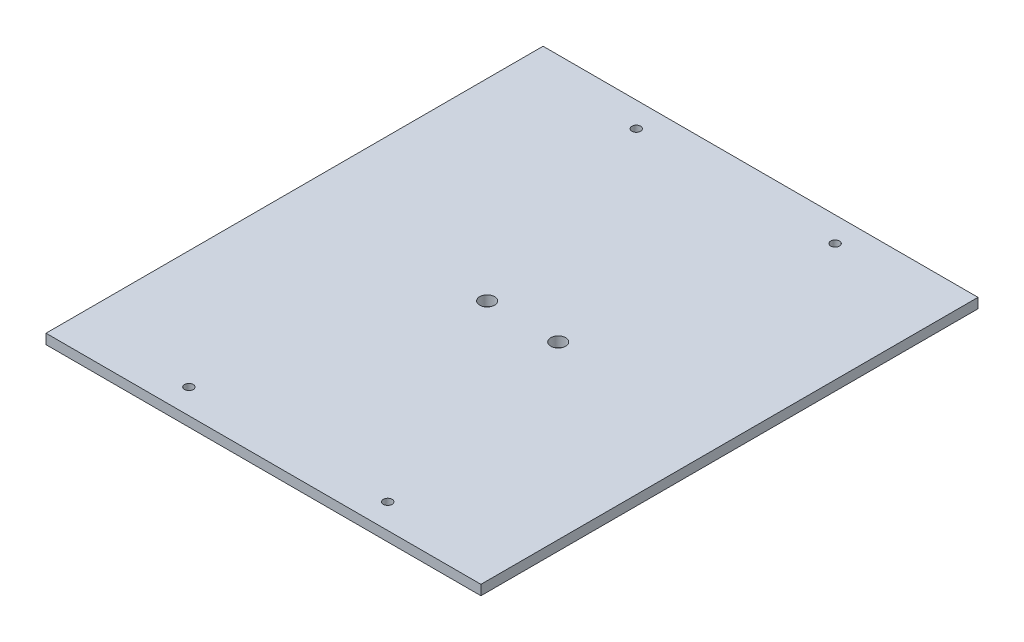
SolidWorks part; units mm, degrees
ref_plane "Front Plane" through (0, 0, 0) normal (0, 0, 1) x (1, 0, 0)
ref_plane "Top Plane" through (0, 0, 0) normal (0, 1, 0) x (1, 0, 0)
ref_plane "Right Plane" through (0, 0, 0) normal (1, 0, 0) x (0, 0, -1)
sketch "Sketch1" plane through (0, 0, 0) normal (0, 1, 0) x (1, 0, 0)
  line L1 (-111.125, -127) -> (111.125, -127)
  line L2 (-111.125, -127) -> (-111.125, 127)
  line L3 (-111.125, 127) -> (111.125, 127)
  line L4 (111.125, -127) -> (111.125, 127)
  line L5 (-111.125, -127) -> (111.125, 127) construction
  line L6 (-111.125, 127) -> (111.125, -127) construction
  point P0 (0, 0)
  dimension "D1" = 254
  dimension "D2" = 222.25
extrude "Boss-Extrude1" add sketch "Sketch1" along normal blind 5.08
sketch "Sketch2" plane through (0, 0, 0) normal (0, 1, 0) x (1, 0, 0)
  line L0 (-12.7, 0) -> (23.622, 0) construction
  circle A0 centre (-12.7, 0) radius 3.81
  circle A1 centre (23.622, 0) radius 3.81
  dimension "D1" = 36.322
  dimension "D3" = 7.62
  dimension "D2" = 12.7
extrude "Cut-Extrude2" cut sketch "Sketch2" along normal through all
hole_wizard "#8 Clearance Hole1" positions "Sketch3" profile "Sketch4" hole size "#8" standard "ANSI Inch" end condition through all
sketch "Sketch3" plane through (0, 0, 0) normal (0, -1, 0) x (-1, 0, 0)
  line L1 (101.6, -114.3) -> (-101.6, -114.3)
  line L2 (101.6, -114.3) -> (101.6, 114.3)
  line L3 (101.6, 114.3) -> (-101.6, 114.3)
  line L4 (-101.6, -114.3) -> (-101.6, 114.3)
  line L5 (111.125, -127) -> (-111.125, -127) construction
  line L6 (-111.125, -127) -> (-111.125, 127) construction
  line L7 (-111.125, 127) -> (111.125, 127) construction
  line L8 (111.125, 127) -> (111.125, -127) construction
  line L13 (50.8, -114.3) -> (50.8, 114.3) construction
  line L15 (-50.8, -114.3) -> (-50.8, 114.3) construction
  point P0 (50.8, -114.3)
  point P2 (-50.8, -114.3)
  point P8 (-50.8, 114.3)
  point P10 (50.8, 114.3)
  point P402 (0, 0)
  point P403 (0, 0)
  point P404 (0, 0)
  point P405 (0, 0)
  point P406 (0, 0)
  dimension "D1" = 12.7
  dimension "D2" = 9.525
  dimension "D3" = 12.7
  dimension "D4" = 9.525
  dimension "D6" = 101.6
  dimension "D7" = 50.8
sketch "Sketch4" plane through (-50.8, 0, 114.3) normal (1, 0, 0) x (0, 0, -1)
  line L0 (0, 0) -> (0, 5.08)
  line L1 (0, 5.08) -> (2.2479, 5.08)
  line L2 (2.2479, 5.08) -> (2.2479, 0)
  line L5 (2.2479, 0) -> (0, 0)
  line L11 (0, -6.35) -> (0, 107.95) construction
  dimension "Thru Hole Dia." = 4.4958
  dimension "Thru Hole Depth" = 5.08
inserted part "Ballast_Weight" [suppressed]
move or copy body "Body-Move/Copy1" [suppressed] bodies to move or copy 104 placed by mates yes
